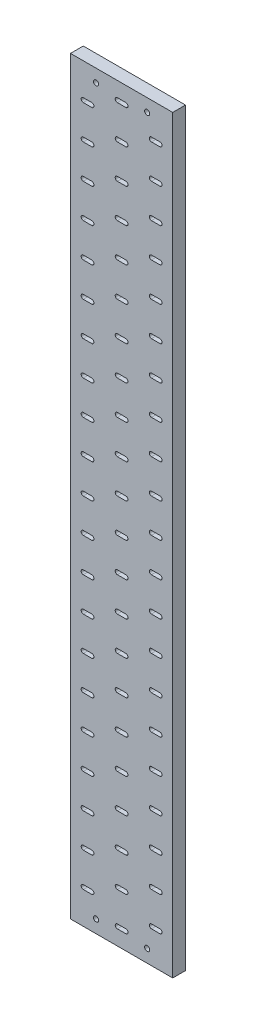
SolidWorks part; units mm, degrees
ref_plane "前视基准面" through (0, 0, 0) normal (0, 0, 1) x (1, 0, 0)
ref_plane "上视基准面" through (0, 0, 0) normal (0, 1, 0) x (1, 0, 0)
ref_plane "右视基准面" through (0, 0, 0) normal (1, 0, 0) x (0, 0, -1)
other "Configuration Table"
sketch "草图1" plane through (0, 0, 0) normal (0, 0, 1) x (1, 0, 0)
  line L9 (544.3012, 492.7441) -> (534.3012, 492.7441)
  line L10 (544.3012, 492.7441) -> (544.3012, 487.7441) construction
  line L11 (544.3012, 487.7441) -> (534.3012, 487.7441)
  line L12 (534.3012, 492.7441) -> (534.3012, 487.7441) construction
  line L14 (464.3012, 492.7441) -> (454.3012, 492.7441)
  line L15 (464.3012, 487.7441) -> (454.3012, 487.7441)
  line L18 (504.3012, 472.7441) -> (494.3012, 472.7441)
  line L19 (504.3012, 467.7441) -> (494.3012, 467.7441)
  line L20 (494.3012, 472.7441) -> (494.3012, 467.7441) construction
  line L21 (504.3012, 472.7441) -> (504.3012, 467.7441) construction
  line L22 (464.3012, 492.7441) -> (464.3012, 487.7441) construction
  line L23 (454.3012, 492.7441) -> (454.3012, 487.7441) construction
  line L24 (559.3012, 530.2441) -> (559.3012, -349.7559)
  line L25 (499.3012, 474.0701) -> (499.3012, 484.8153) construction
  line L26 (559.3012, 530.2441) -> (439.3012, 530.2441)
  line L27 (559.3012, -349.7559) -> (439.3012, -349.7559)
  line L28 (439.3012, 530.2441) -> (439.3012, -349.7559)
  line L29 (439.3012, 500.2441) -> (559.3012, 500.2441) construction
  line L30 (504.3012, 512.7441) -> (494.3012, 512.7441)
  line L31 (504.3012, 507.7441) -> (494.3012, 507.7441)
  line L32 (559.3012, 570.2441) -> (559.3012, -309.7559)
  line L33 (494.3012, 512.7441) -> (494.3012, 507.7441) construction
  line L34 (504.3012, 512.7441) -> (504.3012, 507.7441) construction
  line L35 (544.3012, 452.7441) -> (534.3012, 452.7441)
  line L36 (544.3012, 447.7441) -> (534.3012, 447.7441)
  line L37 (464.3012, 452.7441) -> (454.3012, 452.7441)
  line L38 (464.3012, 447.7441) -> (454.3012, 447.7441)
  line L39 (504.3012, 432.7441) -> (494.3012, 432.7441)
  line L40 (504.3012, 427.7441) -> (494.3012, 427.7441)
  line L41 (544.3012, 452.7441) -> (544.3012, 447.7441) construction
  line L42 (534.3012, 452.7441) -> (534.3012, 447.7441) construction
  line L43 (494.3012, 432.7441) -> (494.3012, 427.7441) construction
  line L44 (504.3012, 432.7441) -> (504.3012, 427.7441) construction
  line L45 (464.3012, 452.7441) -> (464.3012, 447.7441) construction
  line L46 (454.3012, 452.7441) -> (454.3012, 447.7441) construction
  line L47 (544.3012, 412.7441) -> (534.3012, 412.7441)
  line L48 (544.3012, 407.7441) -> (534.3012, 407.7441)
  line L49 (464.3012, 412.7441) -> (454.3012, 412.7441)
  line L50 (464.3012, 407.7441) -> (454.3012, 407.7441)
  line L51 (504.3012, 392.7441) -> (494.3012, 392.7441)
  line L52 (504.3012, 387.7441) -> (494.3012, 387.7441)
  line L53 (544.3012, 412.7441) -> (544.3012, 407.7441) construction
  line L54 (534.3012, 412.7441) -> (534.3012, 407.7441) construction
  line L55 (494.3012, 392.7441) -> (494.3012, 387.7441) construction
  line L56 (504.3012, 392.7441) -> (504.3012, 387.7441) construction
  line L57 (464.3012, 412.7441) -> (464.3012, 407.7441) construction
  line L58 (454.3012, 412.7441) -> (454.3012, 407.7441) construction
  line L59 (544.3012, 372.7441) -> (534.3012, 372.7441)
  line L60 (544.3012, 367.7441) -> (534.3012, 367.7441)
  line L61 (464.3012, 372.7441) -> (454.3012, 372.7441)
  line L62 (464.3012, 367.7441) -> (454.3012, 367.7441)
  line L63 (504.3012, 352.7441) -> (494.3012, 352.7441)
  line L64 (504.3012, 347.7441) -> (494.3012, 347.7441)
  line L65 (544.3012, 372.7441) -> (544.3012, 367.7441) construction
  line L66 (534.3012, 372.7441) -> (534.3012, 367.7441) construction
  line L67 (494.3012, 352.7441) -> (494.3012, 347.7441) construction
  line L68 (504.3012, 352.7441) -> (504.3012, 347.7441) construction
  line L69 (464.3012, 372.7441) -> (464.3012, 367.7441) construction
  line L70 (454.3012, 372.7441) -> (454.3012, 367.7441) construction
  line L71 (544.3012, 332.7441) -> (534.3012, 332.7441)
  line L72 (544.3012, 327.7441) -> (534.3012, 327.7441)
  line L73 (464.3012, 332.7441) -> (454.3012, 332.7441)
  line L74 (464.3012, 327.7441) -> (454.3012, 327.7441)
  line L75 (504.3012, 312.7441) -> (494.3012, 312.7441)
  line L76 (504.3012, 307.7441) -> (494.3012, 307.7441)
  line L77 (544.3012, 332.7441) -> (544.3012, 327.7441) construction
  line L78 (534.3012, 332.7441) -> (534.3012, 327.7441) construction
  line L79 (494.3012, 312.7441) -> (494.3012, 307.7441) construction
  line L80 (504.3012, 312.7441) -> (504.3012, 307.7441) construction
  line L81 (464.3012, 332.7441) -> (464.3012, 327.7441) construction
  line L82 (454.3012, 332.7441) -> (454.3012, 327.7441) construction
  line L83 (544.3012, 292.7441) -> (534.3012, 292.7441)
  line L84 (544.3012, 287.7441) -> (534.3012, 287.7441)
  line L85 (464.3012, 292.7441) -> (454.3012, 292.7441)
  line L86 (464.3012, 287.7441) -> (454.3012, 287.7441)
  line L87 (504.3012, 272.7441) -> (494.3012, 272.7441)
  line L88 (504.3012, 267.7441) -> (494.3012, 267.7441)
  line L89 (544.3012, 292.7441) -> (544.3012, 287.7441) construction
  line L90 (534.3012, 292.7441) -> (534.3012, 287.7441) construction
  line L91 (494.3012, 272.7441) -> (494.3012, 267.7441) construction
  line L92 (504.3012, 272.7441) -> (504.3012, 267.7441) construction
  line L93 (464.3012, 292.7441) -> (464.3012, 287.7441) construction
  line L94 (454.3012, 292.7441) -> (454.3012, 287.7441) construction
  line L95 (544.3012, 252.7441) -> (534.3012, 252.7441)
  line L96 (544.3012, 247.7441) -> (534.3012, 247.7441)
  line L97 (464.3012, 252.7441) -> (454.3012, 252.7441)
  line L98 (464.3012, 247.7441) -> (454.3012, 247.7441)
  line L99 (504.3012, 232.7441) -> (494.3012, 232.7441)
  line L100 (504.3012, 227.7441) -> (494.3012, 227.7441)
  line L101 (544.3012, 252.7441) -> (544.3012, 247.7441) construction
  line L102 (534.3012, 252.7441) -> (534.3012, 247.7441) construction
  line L103 (494.3012, 232.7441) -> (494.3012, 227.7441) construction
  line L104 (504.3012, 232.7441) -> (504.3012, 227.7441) construction
  line L105 (464.3012, 252.7441) -> (464.3012, 247.7441) construction
  line L106 (454.3012, 252.7441) -> (454.3012, 247.7441) construction
  line L107 (544.3012, 212.7441) -> (534.3012, 212.7441)
  line L108 (544.3012, 207.7441) -> (534.3012, 207.7441)
  line L109 (464.3012, 212.7441) -> (454.3012, 212.7441)
  line L110 (464.3012, 207.7441) -> (454.3012, 207.7441)
  line L111 (504.3012, 192.7441) -> (494.3012, 192.7441)
  line L112 (504.3012, 187.7441) -> (494.3012, 187.7441)
  line L113 (544.3012, 212.7441) -> (544.3012, 207.7441) construction
  line L114 (534.3012, 212.7441) -> (534.3012, 207.7441) construction
  line L115 (494.3012, 192.7441) -> (494.3012, 187.7441) construction
  line L116 (504.3012, 192.7441) -> (504.3012, 187.7441) construction
  line L117 (464.3012, 212.7441) -> (464.3012, 207.7441) construction
  line L118 (454.3012, 212.7441) -> (454.3012, 207.7441) construction
  line L119 (544.3012, 172.7441) -> (534.3012, 172.7441)
  line L120 (544.3012, 167.7441) -> (534.3012, 167.7441)
  line L121 (464.3012, 172.7441) -> (454.3012, 172.7441)
  line L122 (464.3012, 167.7441) -> (454.3012, 167.7441)
  line L123 (504.3012, 152.7441) -> (494.3012, 152.7441)
  line L124 (504.3012, 147.7441) -> (494.3012, 147.7441)
  line L125 (544.3012, 172.7441) -> (544.3012, 167.7441) construction
  line L126 (534.3012, 172.7441) -> (534.3012, 167.7441) construction
  line L127 (494.3012, 152.7441) -> (494.3012, 147.7441) construction
  line L128 (504.3012, 152.7441) -> (504.3012, 147.7441) construction
  line L129 (464.3012, 172.7441) -> (464.3012, 167.7441) construction
  line L130 (454.3012, 172.7441) -> (454.3012, 167.7441) construction
  line L131 (544.3012, 132.7441) -> (534.3012, 132.7441)
  line L132 (544.3012, 127.7441) -> (534.3012, 127.7441)
  line L133 (464.3012, 132.7441) -> (454.3012, 132.7441)
  line L134 (464.3012, 127.7441) -> (454.3012, 127.7441)
  line L135 (504.3012, 112.7441) -> (494.3012, 112.7441)
  line L136 (504.3012, 107.7441) -> (494.3012, 107.7441)
  line L137 (544.3012, 132.7441) -> (544.3012, 127.7441) construction
  line L138 (534.3012, 132.7441) -> (534.3012, 127.7441) construction
  line L139 (494.3012, 112.7441) -> (494.3012, 107.7441) construction
  line L140 (504.3012, 112.7441) -> (504.3012, 107.7441) construction
  line L141 (464.3012, 132.7441) -> (464.3012, 127.7441) construction
  line L142 (454.3012, 132.7441) -> (454.3012, 127.7441) construction
  line L143 (544.3012, 92.7441) -> (534.3012, 92.7441)
  line L144 (544.3012, 87.7441) -> (534.3012, 87.7441)
  line L145 (464.3012, 92.7441) -> (454.3012, 92.7441)
  line L146 (464.3012, 87.7441) -> (454.3012, 87.7441)
  line L147 (504.3012, 72.7441) -> (494.3012, 72.7441)
  line L148 (504.3012, 67.7441) -> (494.3012, 67.7441)
  line L149 (544.3012, 92.7441) -> (544.3012, 87.7441) construction
  line L150 (534.3012, 92.7441) -> (534.3012, 87.7441) construction
  line L151 (494.3012, 72.7441) -> (494.3012, 67.7441) construction
  line L152 (504.3012, 72.7441) -> (504.3012, 67.7441) construction
  line L153 (464.3012, 92.7441) -> (464.3012, 87.7441) construction
  line L154 (454.3012, 92.7441) -> (454.3012, 87.7441) construction
  line L155 (544.3012, 52.7441) -> (534.3012, 52.7441)
  line L156 (544.3012, 47.7441) -> (534.3012, 47.7441)
  line L157 (464.3012, 52.7441) -> (454.3012, 52.7441)
  line L158 (464.3012, 47.7441) -> (454.3012, 47.7441)
  line L159 (504.3012, 32.7441) -> (494.3012, 32.7441)
  line L160 (504.3012, 27.7441) -> (494.3012, 27.7441)
  line L161 (544.3012, 52.7441) -> (544.3012, 47.7441) construction
  line L162 (534.3012, 52.7441) -> (534.3012, 47.7441) construction
  line L163 (494.3012, 32.7441) -> (494.3012, 27.7441) construction
  line L164 (504.3012, 32.7441) -> (504.3012, 27.7441) construction
  line L165 (464.3012, 52.7441) -> (464.3012, 47.7441) construction
  line L166 (454.3012, 52.7441) -> (454.3012, 47.7441) construction
  line L167 (544.3012, 12.7441) -> (534.3012, 12.7441)
  line L168 (544.3012, 7.7441) -> (534.3012, 7.7441)
  line L169 (464.3012, 12.7441) -> (454.3012, 12.7441)
  line L170 (464.3012, 7.7441) -> (454.3012, 7.7441)
  line L171 (504.3012, -7.2559) -> (494.3012, -7.2559)
  line L172 (504.3012, -12.2559) -> (494.3012, -12.2559)
  line L173 (544.3012, 12.7441) -> (544.3012, 7.7441) construction
  line L174 (534.3012, 12.7441) -> (534.3012, 7.7441) construction
  line L175 (494.3012, -7.2559) -> (494.3012, -12.2559) construction
  line L176 (504.3012, -7.2559) -> (504.3012, -12.2559) construction
  line L177 (464.3012, 12.7441) -> (464.3012, 7.7441) construction
  line L178 (454.3012, 12.7441) -> (454.3012, 7.7441) construction
  line L179 (544.3012, -27.2559) -> (534.3012, -27.2559)
  line L180 (544.3012, -32.2559) -> (534.3012, -32.2559)
  line L181 (464.3012, -27.2559) -> (454.3012, -27.2559)
  line L182 (464.3012, -32.2559) -> (454.3012, -32.2559)
  line L183 (504.3012, -47.2559) -> (494.3012, -47.2559)
  line L184 (504.3012, -52.2559) -> (494.3012, -52.2559)
  line L185 (544.3012, -27.2559) -> (544.3012, -32.2559) construction
  line L186 (534.3012, -27.2559) -> (534.3012, -32.2559) construction
  line L187 (494.3012, -47.2559) -> (494.3012, -52.2559) construction
  line L188 (504.3012, -47.2559) -> (504.3012, -52.2559) construction
  line L189 (464.3012, -27.2559) -> (464.3012, -32.2559) construction
  line L190 (454.3012, -27.2559) -> (454.3012, -32.2559) construction
  line L191 (544.3012, -67.2559) -> (534.3012, -67.2559)
  line L192 (544.3012, -72.2559) -> (534.3012, -72.2559)
  line L193 (464.3012, -67.2559) -> (454.3012, -67.2559)
  line L194 (464.3012, -72.2559) -> (454.3012, -72.2559)
  line L195 (504.3012, -87.2559) -> (494.3012, -87.2559)
  line L196 (504.3012, -92.2559) -> (494.3012, -92.2559)
  line L197 (544.3012, -67.2559) -> (544.3012, -72.2559) construction
  line L198 (534.3012, -67.2559) -> (534.3012, -72.2559) construction
  line L199 (494.3012, -87.2559) -> (494.3012, -92.2559) construction
  line L200 (504.3012, -87.2559) -> (504.3012, -92.2559) construction
  line L201 (464.3012, -67.2559) -> (464.3012, -72.2559) construction
  line L202 (454.3012, -67.2559) -> (454.3012, -72.2559) construction
  line L203 (544.3012, -107.2559) -> (534.3012, -107.2559)
  line L204 (544.3012, -112.2559) -> (534.3012, -112.2559)
  line L205 (464.3012, -107.2559) -> (454.3012, -107.2559)
  line L206 (464.3012, -112.2559) -> (454.3012, -112.2559)
  line L207 (504.3012, -127.2559) -> (494.3012, -127.2559)
  line L208 (504.3012, -132.2559) -> (494.3012, -132.2559)
  line L209 (544.3012, -107.2559) -> (544.3012, -112.2559) construction
  line L210 (534.3012, -107.2559) -> (534.3012, -112.2559) construction
  line L211 (494.3012, -127.2559) -> (494.3012, -132.2559) construction
  line L212 (504.3012, -127.2559) -> (504.3012, -132.2559) construction
  line L213 (464.3012, -107.2559) -> (464.3012, -112.2559) construction
  line L214 (454.3012, -107.2559) -> (454.3012, -112.2559) construction
  line L215 (544.3012, -147.2559) -> (534.3012, -147.2559)
  line L216 (544.3012, -152.2559) -> (534.3012, -152.2559)
  line L217 (464.3012, -147.2559) -> (454.3012, -147.2559)
  line L218 (464.3012, -152.2559) -> (454.3012, -152.2559)
  line L219 (504.3012, -167.2559) -> (494.3012, -167.2559)
  line L220 (504.3012, -172.2559) -> (494.3012, -172.2559)
  line L221 (544.3012, -147.2559) -> (544.3012, -152.2559) construction
  line L222 (534.3012, -147.2559) -> (534.3012, -152.2559) construction
  line L223 (494.3012, -167.2559) -> (494.3012, -172.2559) construction
  line L224 (504.3012, -167.2559) -> (504.3012, -172.2559) construction
  line L225 (464.3012, -147.2559) -> (464.3012, -152.2559) construction
  line L226 (454.3012, -147.2559) -> (454.3012, -152.2559) construction
  line L227 (544.3012, -187.2559) -> (534.3012, -187.2559)
  line L228 (544.3012, -192.2559) -> (534.3012, -192.2559)
  line L229 (464.3012, -187.2559) -> (454.3012, -187.2559)
  line L230 (464.3012, -192.2559) -> (454.3012, -192.2559)
  line L231 (504.3012, -207.2559) -> (494.3012, -207.2559)
  line L232 (504.3012, -212.2559) -> (494.3012, -212.2559)
  line L233 (544.3012, -187.2559) -> (544.3012, -192.2559) construction
  line L234 (534.3012, -187.2559) -> (534.3012, -192.2559) construction
  line L235 (494.3012, -207.2559) -> (494.3012, -212.2559) construction
  line L236 (504.3012, -207.2559) -> (504.3012, -212.2559) construction
  line L237 (464.3012, -187.2559) -> (464.3012, -192.2559) construction
  line L238 (454.3012, -187.2559) -> (454.3012, -192.2559) construction
  line L239 (544.3012, -227.2559) -> (534.3012, -227.2559)
  line L240 (544.3012, -232.2559) -> (534.3012, -232.2559)
  line L241 (464.3012, -227.2559) -> (454.3012, -227.2559)
  line L242 (464.3012, -232.2559) -> (454.3012, -232.2559)
  line L243 (504.3012, -247.2559) -> (494.3012, -247.2559)
  line L244 (504.3012, -252.2559) -> (494.3012, -252.2559)
  line L245 (544.3012, -227.2559) -> (544.3012, -232.2559) construction
  line L246 (534.3012, -227.2559) -> (534.3012, -232.2559) construction
  line L247 (494.3012, -247.2559) -> (494.3012, -252.2559) construction
  line L248 (504.3012, -247.2559) -> (504.3012, -252.2559) construction
  line L249 (464.3012, -227.2559) -> (464.3012, -232.2559) construction
  line L250 (454.3012, -227.2559) -> (454.3012, -232.2559) construction
  line L251 (544.3012, -267.2559) -> (534.3012, -267.2559)
  line L252 (544.3012, -272.2559) -> (534.3012, -272.2559)
  line L253 (464.3012, -267.2559) -> (454.3012, -267.2559)
  line L254 (464.3012, -272.2559) -> (454.3012, -272.2559)
  line L255 (504.3012, -287.2559) -> (494.3012, -287.2559)
  line L256 (504.3012, -292.2559) -> (494.3012, -292.2559)
  line L257 (544.3012, -267.2559) -> (544.3012, -272.2559) construction
  line L258 (534.3012, -267.2559) -> (534.3012, -272.2559) construction
  line L259 (494.3012, -287.2559) -> (494.3012, -292.2559) construction
  line L260 (504.3012, -287.2559) -> (504.3012, -292.2559) construction
  line L261 (464.3012, -267.2559) -> (464.3012, -272.2559) construction
  line L262 (454.3012, -267.2559) -> (454.3012, -272.2559) construction
  line L263 (544.3012, -307.2559) -> (534.3012, -307.2559)
  line L264 (544.3012, -312.2559) -> (534.3012, -312.2559)
  line L265 (464.3012, -307.2559) -> (454.3012, -307.2559)
  line L266 (464.3012, -312.2559) -> (454.3012, -312.2559)
  line L267 (504.3012, -327.2559) -> (494.3012, -327.2559)
  line L268 (504.3012, -332.2559) -> (494.3012, -332.2559)
  line L269 (544.3012, -307.2559) -> (544.3012, -312.2559) construction
  line L270 (534.3012, -307.2559) -> (534.3012, -312.2559) construction
  line L271 (494.3012, -327.2559) -> (494.3012, -332.2559) construction
  line L272 (504.3012, -327.2559) -> (504.3012, -332.2559) construction
  line L273 (464.3012, -307.2559) -> (464.3012, -312.2559) construction
  line L274 (454.3012, -307.2559) -> (454.3012, -312.2559) construction
  arc A2 (544.3012, 487.7441) -> (544.3012, 492.7441) centre (544.3012, 490.2441) ccw
  arc A3 (534.3012, 492.7441) -> (534.3012, 487.7441) centre (534.3012, 490.2441) ccw
  arc A8 (504.3012, 467.7441) -> (504.3012, 472.7441) centre (504.3012, 470.2441) ccw
  arc A9 (494.3012, 472.7441) -> (494.3012, 467.7441) centre (494.3012, 470.2441) ccw
  arc A10 (464.3012, 487.7441) -> (464.3012, 492.7441) centre (464.3012, 490.2441) ccw
  arc A11 (454.3012, 492.7441) -> (454.3012, 487.7441) centre (454.3012, 490.2441) ccw
  circle A222 centre (529.3012, 515.2441) radius 3
  arc A223 (504.3012, 507.7441) -> (504.3012, 512.7441) centre (504.3012, 510.2441) ccw
  arc A224 (494.3012, 512.7441) -> (494.3012, 507.7441) centre (494.3012, 510.2441) ccw
  arc A225 (544.3012, 447.7441) -> (544.3012, 452.7441) centre (544.3012, 450.2441) ccw
  arc A226 (534.3012, 452.7441) -> (534.3012, 447.7441) centre (534.3012, 450.2441) ccw
  arc A227 (504.3012, 427.7441) -> (504.3012, 432.7441) centre (504.3012, 430.2441) ccw
  arc A228 (494.3012, 432.7441) -> (494.3012, 427.7441) centre (494.3012, 430.2441) ccw
  arc A229 (464.3012, 447.7441) -> (464.3012, 452.7441) centre (464.3012, 450.2441) ccw
  arc A230 (454.3012, 452.7441) -> (454.3012, 447.7441) centre (454.3012, 450.2441) ccw
  arc A231 (544.3012, 407.7441) -> (544.3012, 412.7441) centre (544.3012, 410.2441) ccw
  arc A232 (534.3012, 412.7441) -> (534.3012, 407.7441) centre (534.3012, 410.2441) ccw
  arc A233 (504.3012, 387.7441) -> (504.3012, 392.7441) centre (504.3012, 390.2441) ccw
  arc A234 (494.3012, 392.7441) -> (494.3012, 387.7441) centre (494.3012, 390.2441) ccw
  arc A235 (464.3012, 407.7441) -> (464.3012, 412.7441) centre (464.3012, 410.2441) ccw
  arc A236 (454.3012, 412.7441) -> (454.3012, 407.7441) centre (454.3012, 410.2441) ccw
  arc A237 (544.3012, 367.7441) -> (544.3012, 372.7441) centre (544.3012, 370.2441) ccw
  arc A238 (534.3012, 372.7441) -> (534.3012, 367.7441) centre (534.3012, 370.2441) ccw
  arc A239 (504.3012, 347.7441) -> (504.3012, 352.7441) centre (504.3012, 350.2441) ccw
  arc A240 (494.3012, 352.7441) -> (494.3012, 347.7441) centre (494.3012, 350.2441) ccw
  arc A241 (464.3012, 367.7441) -> (464.3012, 372.7441) centre (464.3012, 370.2441) ccw
  arc A242 (454.3012, 372.7441) -> (454.3012, 367.7441) centre (454.3012, 370.2441) ccw
  arc A243 (544.3012, 327.7441) -> (544.3012, 332.7441) centre (544.3012, 330.2441) ccw
  arc A244 (534.3012, 332.7441) -> (534.3012, 327.7441) centre (534.3012, 330.2441) ccw
  arc A245 (504.3012, 307.7441) -> (504.3012, 312.7441) centre (504.3012, 310.2441) ccw
  arc A246 (494.3012, 312.7441) -> (494.3012, 307.7441) centre (494.3012, 310.2441) ccw
  arc A247 (464.3012, 327.7441) -> (464.3012, 332.7441) centre (464.3012, 330.2441) ccw
  arc A248 (454.3012, 332.7441) -> (454.3012, 327.7441) centre (454.3012, 330.2441) ccw
  arc A249 (544.3012, 287.7441) -> (544.3012, 292.7441) centre (544.3012, 290.2441) ccw
  arc A250 (534.3012, 292.7441) -> (534.3012, 287.7441) centre (534.3012, 290.2441) ccw
  arc A251 (504.3012, 267.7441) -> (504.3012, 272.7441) centre (504.3012, 270.2441) ccw
  arc A252 (494.3012, 272.7441) -> (494.3012, 267.7441) centre (494.3012, 270.2441) ccw
  arc A253 (464.3012, 287.7441) -> (464.3012, 292.7441) centre (464.3012, 290.2441) ccw
  arc A254 (454.3012, 292.7441) -> (454.3012, 287.7441) centre (454.3012, 290.2441) ccw
  arc A255 (544.3012, 247.7441) -> (544.3012, 252.7441) centre (544.3012, 250.2441) ccw
  arc A256 (534.3012, 252.7441) -> (534.3012, 247.7441) centre (534.3012, 250.2441) ccw
  arc A257 (504.3012, 227.7441) -> (504.3012, 232.7441) centre (504.3012, 230.2441) ccw
  arc A258 (494.3012, 232.7441) -> (494.3012, 227.7441) centre (494.3012, 230.2441) ccw
  arc A259 (464.3012, 247.7441) -> (464.3012, 252.7441) centre (464.3012, 250.2441) ccw
  arc A260 (454.3012, 252.7441) -> (454.3012, 247.7441) centre (454.3012, 250.2441) ccw
  arc A261 (544.3012, 207.7441) -> (544.3012, 212.7441) centre (544.3012, 210.2441) ccw
  arc A262 (534.3012, 212.7441) -> (534.3012, 207.7441) centre (534.3012, 210.2441) ccw
  arc A263 (504.3012, 187.7441) -> (504.3012, 192.7441) centre (504.3012, 190.2441) ccw
  arc A264 (494.3012, 192.7441) -> (494.3012, 187.7441) centre (494.3012, 190.2441) ccw
  arc A265 (464.3012, 207.7441) -> (464.3012, 212.7441) centre (464.3012, 210.2441) ccw
  arc A266 (454.3012, 212.7441) -> (454.3012, 207.7441) centre (454.3012, 210.2441) ccw
  arc A267 (544.3012, 167.7441) -> (544.3012, 172.7441) centre (544.3012, 170.2441) ccw
  arc A268 (534.3012, 172.7441) -> (534.3012, 167.7441) centre (534.3012, 170.2441) ccw
  arc A269 (504.3012, 147.7441) -> (504.3012, 152.7441) centre (504.3012, 150.2441) ccw
  arc A270 (494.3012, 152.7441) -> (494.3012, 147.7441) centre (494.3012, 150.2441) ccw
  arc A271 (464.3012, 167.7441) -> (464.3012, 172.7441) centre (464.3012, 170.2441) ccw
  arc A272 (454.3012, 172.7441) -> (454.3012, 167.7441) centre (454.3012, 170.2441) ccw
  arc A273 (544.3012, 127.7441) -> (544.3012, 132.7441) centre (544.3012, 130.2441) ccw
  arc A274 (534.3012, 132.7441) -> (534.3012, 127.7441) centre (534.3012, 130.2441) ccw
  arc A275 (504.3012, 107.7441) -> (504.3012, 112.7441) centre (504.3012, 110.2441) ccw
  arc A276 (494.3012, 112.7441) -> (494.3012, 107.7441) centre (494.3012, 110.2441) ccw
  arc A277 (464.3012, 127.7441) -> (464.3012, 132.7441) centre (464.3012, 130.2441) ccw
  arc A278 (454.3012, 132.7441) -> (454.3012, 127.7441) centre (454.3012, 130.2441) ccw
  arc A279 (544.3012, 87.7441) -> (544.3012, 92.7441) centre (544.3012, 90.2441) ccw
  arc A280 (534.3012, 92.7441) -> (534.3012, 87.7441) centre (534.3012, 90.2441) ccw
  arc A281 (504.3012, 67.7441) -> (504.3012, 72.7441) centre (504.3012, 70.2441) ccw
  arc A282 (494.3012, 72.7441) -> (494.3012, 67.7441) centre (494.3012, 70.2441) ccw
  arc A283 (464.3012, 87.7441) -> (464.3012, 92.7441) centre (464.3012, 90.2441) ccw
  arc A284 (454.3012, 92.7441) -> (454.3012, 87.7441) centre (454.3012, 90.2441) ccw
  arc A285 (544.3012, 47.7441) -> (544.3012, 52.7441) centre (544.3012, 50.2441) ccw
  arc A286 (534.3012, 52.7441) -> (534.3012, 47.7441) centre (534.3012, 50.2441) ccw
  arc A287 (504.3012, 27.7441) -> (504.3012, 32.7441) centre (504.3012, 30.2441) ccw
  arc A288 (494.3012, 32.7441) -> (494.3012, 27.7441) centre (494.3012, 30.2441) ccw
  arc A289 (464.3012, 47.7441) -> (464.3012, 52.7441) centre (464.3012, 50.2441) ccw
  arc A290 (454.3012, 52.7441) -> (454.3012, 47.7441) centre (454.3012, 50.2441) ccw
  arc A291 (544.3012, 7.7441) -> (544.3012, 12.7441) centre (544.3012, 10.2441) ccw
  arc A292 (534.3012, 12.7441) -> (534.3012, 7.7441) centre (534.3012, 10.2441) ccw
  arc A293 (504.3012, -12.2559) -> (504.3012, -7.2559) centre (504.3012, -9.7559) ccw
  arc A294 (494.3012, -7.2559) -> (494.3012, -12.2559) centre (494.3012, -9.7559) ccw
  arc A295 (464.3012, 7.7441) -> (464.3012, 12.7441) centre (464.3012, 10.2441) ccw
  arc A296 (454.3012, 12.7441) -> (454.3012, 7.7441) centre (454.3012, 10.2441) ccw
  arc A297 (544.3012, -32.2559) -> (544.3012, -27.2559) centre (544.3012, -29.7559) ccw
  arc A298 (534.3012, -27.2559) -> (534.3012, -32.2559) centre (534.3012, -29.7559) ccw
  arc A299 (504.3012, -52.2559) -> (504.3012, -47.2559) centre (504.3012, -49.7559) ccw
  arc A300 (494.3012, -47.2559) -> (494.3012, -52.2559) centre (494.3012, -49.7559) ccw
  arc A301 (464.3012, -32.2559) -> (464.3012, -27.2559) centre (464.3012, -29.7559) ccw
  arc A302 (454.3012, -27.2559) -> (454.3012, -32.2559) centre (454.3012, -29.7559) ccw
  arc A303 (544.3012, -72.2559) -> (544.3012, -67.2559) centre (544.3012, -69.7559) ccw
  arc A304 (534.3012, -67.2559) -> (534.3012, -72.2559) centre (534.3012, -69.7559) ccw
  arc A305 (504.3012, -92.2559) -> (504.3012, -87.2559) centre (504.3012, -89.7559) ccw
  arc A306 (494.3012, -87.2559) -> (494.3012, -92.2559) centre (494.3012, -89.7559) ccw
  arc A307 (464.3012, -72.2559) -> (464.3012, -67.2559) centre (464.3012, -69.7559) ccw
  arc A308 (454.3012, -67.2559) -> (454.3012, -72.2559) centre (454.3012, -69.7559) ccw
  arc A309 (544.3012, -112.2559) -> (544.3012, -107.2559) centre (544.3012, -109.7559) ccw
  arc A310 (534.3012, -107.2559) -> (534.3012, -112.2559) centre (534.3012, -109.7559) ccw
  arc A311 (504.3012, -132.2559) -> (504.3012, -127.2559) centre (504.3012, -129.7559) ccw
  arc A312 (494.3012, -127.2559) -> (494.3012, -132.2559) centre (494.3012, -129.7559) ccw
  arc A313 (464.3012, -112.2559) -> (464.3012, -107.2559) centre (464.3012, -109.7559) ccw
  arc A314 (454.3012, -107.2559) -> (454.3012, -112.2559) centre (454.3012, -109.7559) ccw
  arc A315 (544.3012, -152.2559) -> (544.3012, -147.2559) centre (544.3012, -149.7559) ccw
  arc A316 (534.3012, -147.2559) -> (534.3012, -152.2559) centre (534.3012, -149.7559) ccw
  arc A317 (504.3012, -172.2559) -> (504.3012, -167.2559) centre (504.3012, -169.7559) ccw
  arc A318 (494.3012, -167.2559) -> (494.3012, -172.2559) centre (494.3012, -169.7559) ccw
  arc A319 (464.3012, -152.2559) -> (464.3012, -147.2559) centre (464.3012, -149.7559) ccw
  arc A320 (454.3012, -147.2559) -> (454.3012, -152.2559) centre (454.3012, -149.7559) ccw
  arc A321 (544.3012, -192.2559) -> (544.3012, -187.2559) centre (544.3012, -189.7559) ccw
  arc A322 (534.3012, -187.2559) -> (534.3012, -192.2559) centre (534.3012, -189.7559) ccw
  arc A323 (504.3012, -212.2559) -> (504.3012, -207.2559) centre (504.3012, -209.7559) ccw
  arc A324 (494.3012, -207.2559) -> (494.3012, -212.2559) centre (494.3012, -209.7559) ccw
  arc A325 (464.3012, -192.2559) -> (464.3012, -187.2559) centre (464.3012, -189.7559) ccw
  arc A326 (454.3012, -187.2559) -> (454.3012, -192.2559) centre (454.3012, -189.7559) ccw
  circle A327 centre (529.3012, -334.7559) radius 3
  circle A328 centre (469.3012, 515.2441) radius 3
  circle A329 centre (469.3012, -334.7559) radius 3
  arc A330 (544.3012, -232.2559) -> (544.3012, -227.2559) centre (544.3012, -229.7559) ccw
  arc A331 (534.3012, -227.2559) -> (534.3012, -232.2559) centre (534.3012, -229.7559) ccw
  arc A332 (504.3012, -252.2559) -> (504.3012, -247.2559) centre (504.3012, -249.7559) ccw
  arc A333 (494.3012, -247.2559) -> (494.3012, -252.2559) centre (494.3012, -249.7559) ccw
  arc A334 (464.3012, -232.2559) -> (464.3012, -227.2559) centre (464.3012, -229.7559) ccw
  arc A335 (454.3012, -227.2559) -> (454.3012, -232.2559) centre (454.3012, -229.7559) ccw
  arc A336 (544.3012, -272.2559) -> (544.3012, -267.2559) centre (544.3012, -269.7559) ccw
  arc A337 (534.3012, -267.2559) -> (534.3012, -272.2559) centre (534.3012, -269.7559) ccw
  arc A338 (504.3012, -292.2559) -> (504.3012, -287.2559) centre (504.3012, -289.7559) ccw
  arc A339 (494.3012, -287.2559) -> (494.3012, -292.2559) centre (494.3012, -289.7559) ccw
  arc A340 (464.3012, -272.2559) -> (464.3012, -267.2559) centre (464.3012, -269.7559) ccw
  arc A341 (454.3012, -267.2559) -> (454.3012, -272.2559) centre (454.3012, -269.7559) ccw
  arc A342 (544.3012, -312.2559) -> (544.3012, -307.2559) centre (544.3012, -309.7559) ccw
  arc A343 (534.3012, -307.2559) -> (534.3012, -312.2559) centre (534.3012, -309.7559) ccw
  arc A344 (504.3012, -332.2559) -> (504.3012, -327.2559) centre (504.3012, -329.7559) ccw
  arc A345 (494.3012, -327.2559) -> (494.3012, -332.2559) centre (494.3012, -329.7559) ccw
  arc A346 (464.3012, -312.2559) -> (464.3012, -307.2559) centre (464.3012, -309.7559) ccw
  arc A347 (454.3012, -307.2559) -> (454.3012, -312.2559) centre (454.3012, -309.7559) ccw
  point P25 (499.3012, -349.7559)
  point P26 (499.3012, 530.2441)
  point P30 (499.3012, 472.7441)
  dimension "D1" = 5
  dimension "D3" = 5
  dimension "D4" = 5
  dimension "D9" = 30
  dimension "D18" = 6
  dimension "D2" = 10
  dimension "D5" = 10
  dimension "D6" = 10
  dimension "D7" = 60
  dimension "D8" = 880
  dimension "D10" = 15
  dimension "D11" = 30
  dimension "D12" = 2
  dimension "D14" = 37.5
  dimension "D15" = 30
  dimension "D16" = 15
  dimension "D13" = 18
  dimension "D17" = 2
  dimension "D19" = 3
extrude "凸台-拉伸1" add sketch "草图1" along normal blind 15 contours L26 L28 L27 L24 A328 A327 A326 L229 A325 L230 A324 L231 A323 L232 A322 L227 A321 L228 A320 L217 A319 L218 A318 L219 A317 L220 A316 L215 A315 L216 A314 L205 A313 L206 A312 L207 A311 L208 A310
